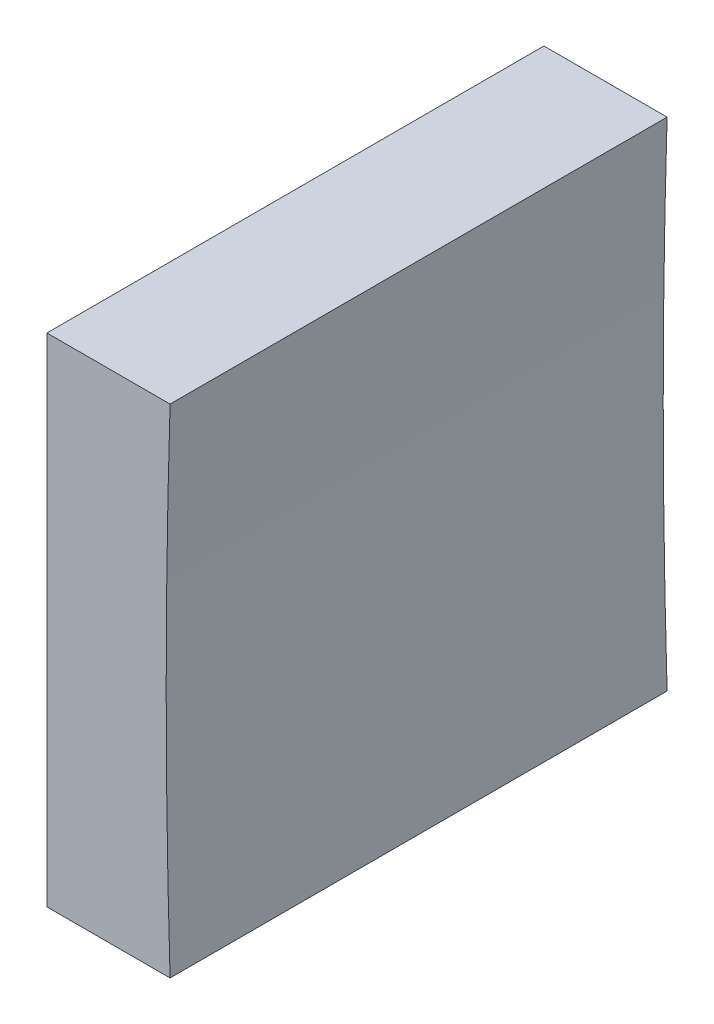
SolidWorks part; units mm, degrees
ref_plane "前视基准面" through (0, 0, 0) normal (0, 0, 1) x (1, 0, 0)
ref_plane "上视基准面" through (0, 0, 0) normal (0, 1, 0) x (1, 0, 0)
ref_plane "右视基准面" through (0, 0, 0) normal (1, 0, 0) x (0, 0, -1)
sketch "草图1" plane through (0, 0, 0) normal (0, 0, 1) x (1, 0, 0)
  line L0 (278.655, 66.8579) -> (298.183, 66.8579) construction
  line L1 (284.7071, 66.8579) -> (284.7071, 79.3579)
  line L2 (284.7071, 79.3579) -> (290.9025, 79.3579)
  line L3 (290.9025, 54.3579) -> (284.7071, 54.3579)
  line L4 (284.7071, 54.3579) -> (284.7071, 66.8579)
  arc A0 (290.9025, 79.3579) -> (290.9025, 54.3579) centre (690.7071, 66.8579) ccw
  dimension "D1" = 400
extrude "凸台-拉伸1" add sketch "草图1" along normal blind 25
